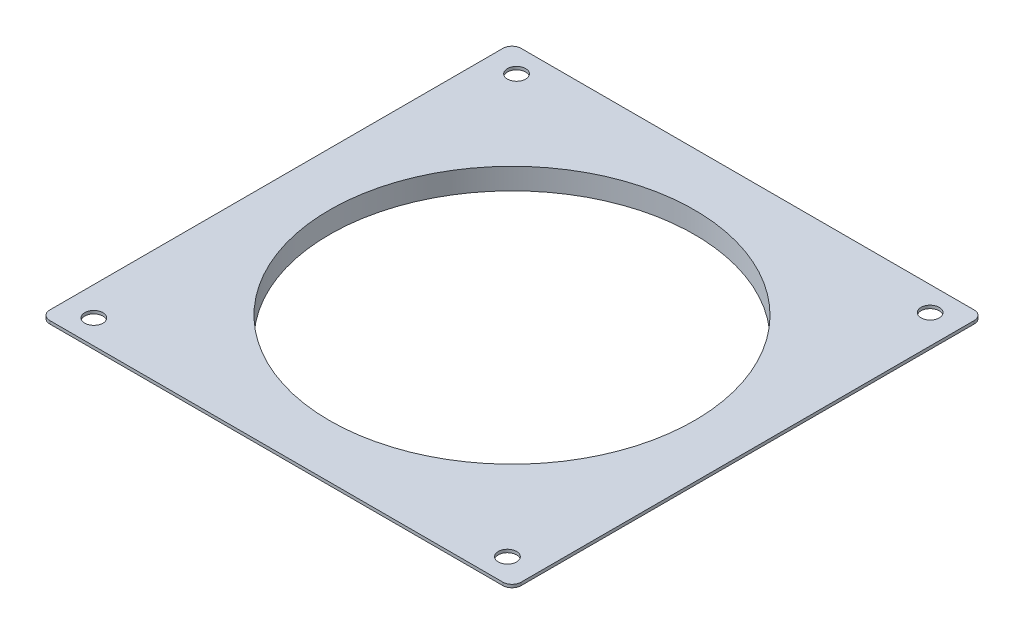
SolidWorks part; units mm, degrees
ref_plane "Front Plane" through (0, 0, 0) normal (0, 0, 1) x (1, 0, 0)
ref_plane "Top Plane" through (0, 0, 0) normal (0, 1, 0) x (1, 0, 0)
ref_plane "Right Plane" through (0, 0, 0) normal (1, 0, 0) x (0, 0, -1)
sketch "Sketch1" plane through (0, 0, 0) normal (0, 1, 0) x (1, 0, 0)
  line L0 (0, 77.5) -> (0, 72.5) construction
  line L1 (-77.5, 77.5) -> (77.5, 77.5)
  line L2 (-77.5, 77.5) -> (-77.5, -77.5)
  line L3 (-77.5, -77.5) -> (77.5, -77.5)
  line L4 (77.5, 77.5) -> (77.5, -77.5)
  line L5 (-65, 72.5) -> (65, 72.5)
  line L6 (-65, 69.5) -> (-65, 72.5) construction
  line L7 (-65, 72.5) -> (-68, 72.5) construction
  line L8 (65, 69.5) -> (65, 72.5) construction
  line L9 (65, 72.5) -> (68, 72.5) construction
  line L10 (-71, 69.5) -> (-77.5, 69.5) construction
  line L11 (71, 69.5) -> (77.5, 69.5) construction
  line L12 (-77.5, 0) -> (77.5, 0) construction
  circle A0 centre (-68, 69.5) radius 3
  circle A1 centre (68, 69.5) radius 3
  circle A2 centre (-68, -69.5) radius 3
  circle A3 centre (68, -69.5) radius 3
  circle A4 centre (0, 0) radius 60
  point P0 (0, 0)
  point P9 (0, 72.5)
  dimension "D5" = 6
  dimension "D6" = 6
  dimension "D7" = 120
  dimension "D1" = 155
  dimension "D2" = 155
  dimension "D3" = 5
  dimension "D4" = 130
extrude "Boss-Extrude1" add sketch "Sketch1" along normal blind 1
fillet "Fillet1" radius 3 4 edges at (-77.5, 0.5, -77.5) (77.5, 0.5, -77.5) (77.5, 0.5, 77.5) (-77.5, 0.5, 77.5)
sketch "Sketch2" plane through (0, 1, 0) normal (0, 1, 0) x (1, 0, 0)
  circle A0 centre (0, 0) radius 60
  circle A1 centre (0, 0) radius 65
  dimension "D1" = 5
extrude "Boss-Extrude2" add sketch "Sketch2" against normal blind 7
